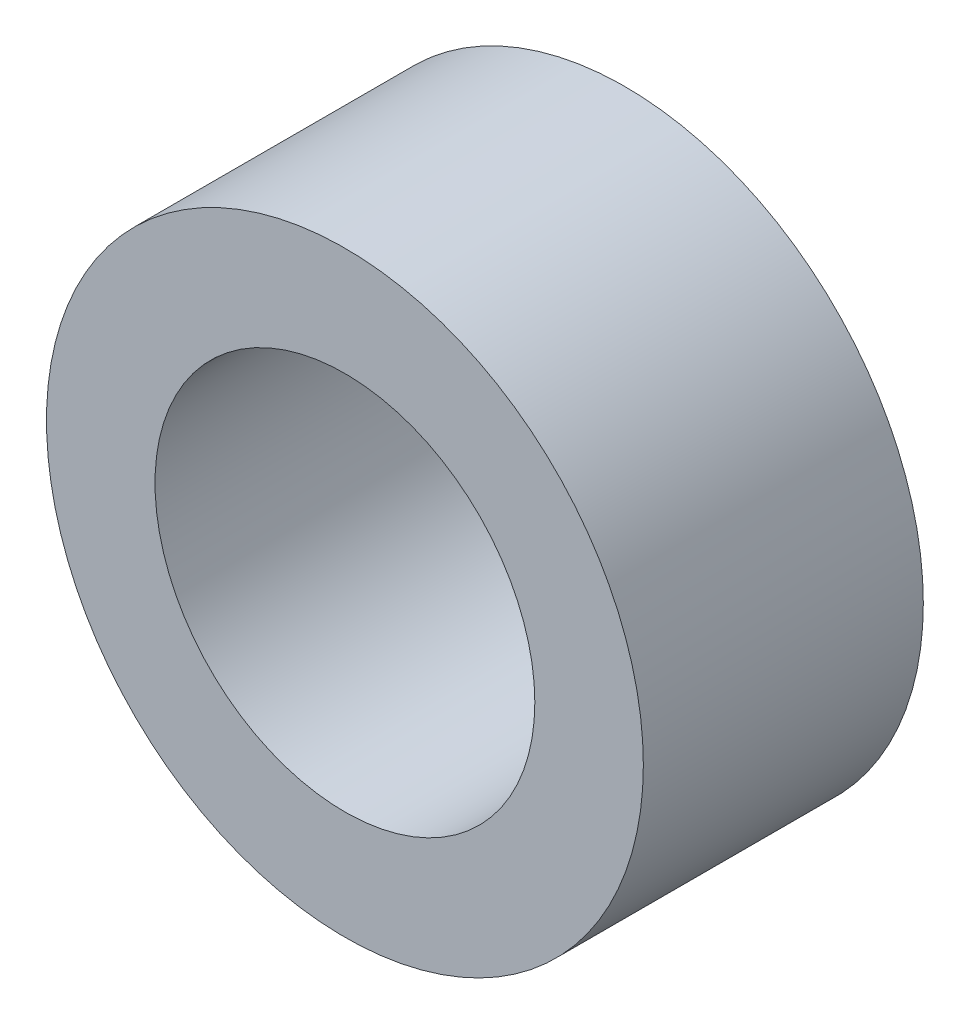
SolidWorks part; units mm, degrees
ref_plane "Front Plane" through (0, 0, 0) normal (0, 0, 1) x (1, 0, 0)
ref_plane "Top Plane" through (0, 0, 0) normal (0, 1, 0) x (1, 0, 0)
ref_plane "Right Plane" through (0, 0, 0) normal (1, 0, 0) x (0, 0, -1)
sketch "Sketch1" plane through (0, 0, 0) normal (0, 0, 1) x (1, 0, 0)
  circle A0 centre (0, 0) radius 13.75
  circle A1 centre (0, 0) radius 8.75
  dimension "D1" = 27.5
  dimension "D2" = 17.5
extrude "Boss-Extrude1" add sketch "Sketch1" along normal blind 12.9
